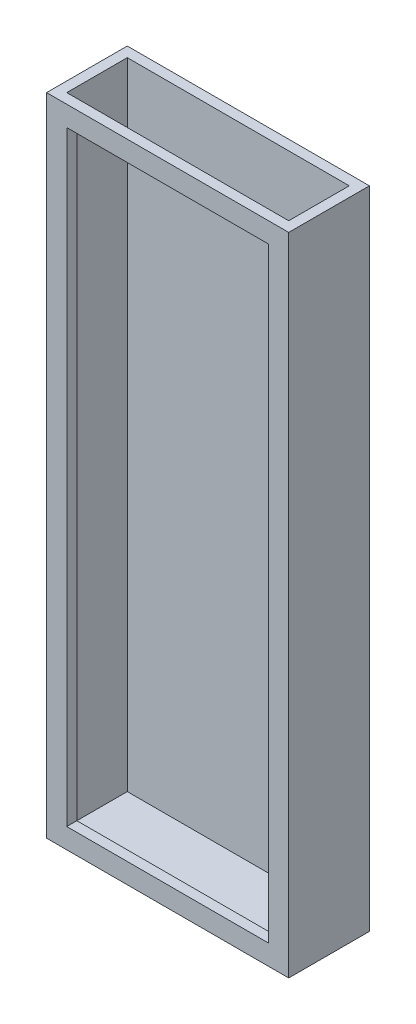
SolidWorks part; units mm, degrees
ref_plane "Front Plane" through (0, 0, 0) normal (0, 0, 1) x (1, 0, 0)
ref_plane "Top Plane" through (0, 0, 0) normal (0, 1, 0) x (1, 0, 0)
ref_plane "Right Plane" through (0, 0, 0) normal (1, 0, 0) x (0, 0, -1)
sketch "Sketch1" plane through (0, 0, 0) normal (0, 1, 0) x (1, 0, 0)
  line L1 (-38.1, 12.7) -> (38.1, 12.7)
  line L2 (-38.1, 12.7) -> (-38.1, -12.7)
  line L3 (-38.1, -12.7) -> (38.1, -12.7)
  line L4 (38.1, 12.7) -> (38.1, -12.7)
  point P0 (0, 0)
  point P6 (0, 0)
  dimension "D1" = 76.2
  dimension "D2" = 25.4
extrude "Boss-Extrude5" add sketch "Sketch1" along normal blind 203.2
sketch "Sketch4" plane through (0, 203.2, 0) normal (0, 1, 0) x (1, 0, 0)
  line L0 (38.1, 12.7) -> (-38.1, 12.7) construction
  line L1 (-34.925, 9.525) -> (34.925, 9.525)
  line L2 (-34.925, 9.525) -> (-34.925, -9.525)
  line L3 (-34.925, -9.525) -> (34.925, -9.525)
  line L4 (34.925, 9.525) -> (34.925, -9.525)
  line L5 (-34.925, 9.525) -> (34.925, -9.525) construction
  line L6 (-34.925, -9.525) -> (34.925, 9.525) construction
  line L7 (-38.1, 12.7) -> (-38.1, -12.7) construction
  point P0 (0, 0)
  dimension "D1" = 3.175
  dimension "D2" = 3.175
extrude "Cut-Extrude1" cut sketch "Sketch4" against normal blind 200.025
sketch "Sketch5" plane through (0, 0, 12.7) normal (0, 0, 1) x (1, 0, 0)
  line L0 (-38.1, 203.2) -> (38.1, 203.2) construction
  line L1 (-31.75, 196.85) -> (31.75, 196.85)
  line L2 (-31.75, 196.85) -> (-31.75, 6.35)
  line L3 (-31.75, 6.35) -> (31.75, 6.35)
  line L4 (31.75, 196.85) -> (31.75, 6.35)
  line L5 (-31.75, 196.85) -> (31.75, 6.35) construction
  line L6 (-31.75, 6.35) -> (31.75, 196.85) construction
  line L7 (-38.1, 203.2) -> (-38.1, 0) construction
  line L8 (38.1, 203.2) -> (38.1, 0) construction
  line L9 (-38.1, 0) -> (38.1, 0) construction
  point P0 (0, 101.6)
  dimension "D1" = 6.35
  dimension "D2" = 6.35
  dimension "D3" = 6.35
  dimension "D4" = 6.35
extrude "Cut-Extrude2" cut sketch "Sketch5" against normal blind 8.89
